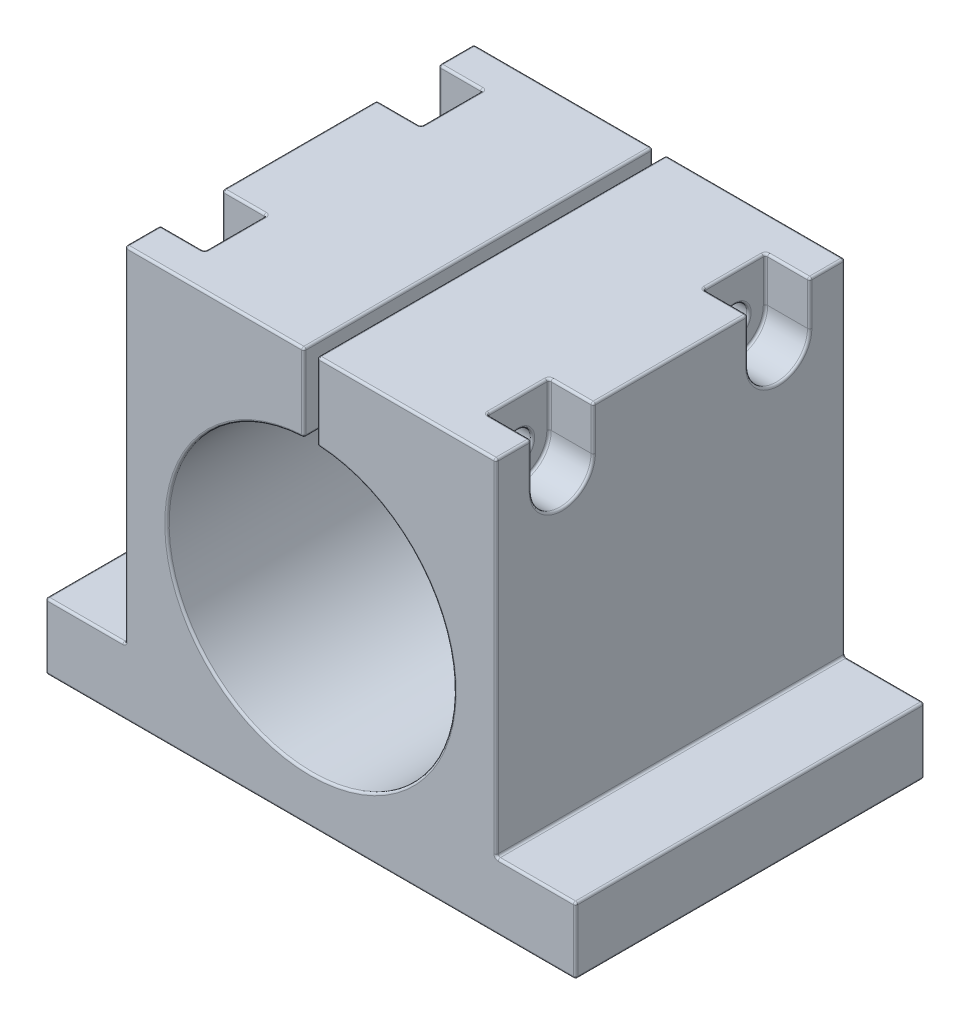
SolidWorks part; units mm, degrees
ref_plane "Спереди" through (0, 0, 0) normal (0, 0, 1) x (1, 0, 0)
ref_plane "Сверху" through (0, 0, 0) normal (0, 1, 0) x (1, 0, 0)
ref_plane "Справа" through (0, 0, 0) normal (1, 0, 0) x (0, 0, -1)
sketch "Эскиз1" plane through (0, 0, 0) normal (0, 0, 1) x (1, 0, 0)
  line L0 (158.9731, 494.9046) -> (1058.9731, 494.9046) construction
  line L1 (0, 0) -> (0, -43) construction
  line L2 (60, -43) -> (-60, -43)
  line L3 (-60, -43) -> (-60, -28)
  line L4 (-60, -28) -> (-42, -28)
  line L5 (-42, -28) -> (-42, 50)
  line L6 (-42, 50) -> (-1.5, 50)
  line L7 (-1.5, 50) -> (-1.5, 32.4654)
  line L8 (1.5, 50) -> (1.5, 32.4654)
  line L9 (42, 50) -> (1.5, 50)
  line L10 (42, -28) -> (42, 50)
  line L11 (60, -28) -> (42, -28)
  line L12 (60, -43) -> (60, -28)
  circle A0 centre (0, 0) radius 32.5
  dimension "D1" = 65
  dimension "D2" = 3
  dimension "D3" = 78
  dimension "D4" = 15
  dimension "D5" = 84
  dimension "D6" = 120
  dimension "D7" = 43
extrude "Бобышка-Вытянуть1" add sketch "Эскиз1" along normal mid plane 79 contours A0 L7 L6 L5 L4 L3 L2 L12 L11 L10 L9 L8
sketch "Эскиз2" plane through (-42, 0, 0) normal (-1, 0, 0) x (0, 0, 1)
  line L0 (39.5, 50) -> (-39.5, 50) construction
  line L1 (-31.5, 50) -> (-17.5, 50)
  line L2 (-31.5, 50) -> (-31.5, 40)
  line L3 (-31.5, 40) -> (-17.5, 40)
  line L4 (-17.5, 50) -> (-17.5, 40)
  line L5 (-39.5, -28) -> (-39.5, 50) construction
  line L6 (17.5, 50) -> (31.5, 50)
  line L7 (17.5, 50) -> (17.5, 40)
  line L8 (17.5, 40) -> (31.5, 40)
  line L9 (31.5, 50) -> (31.5, 40)
  line L10 (39.5, -28) -> (39.5, 50) construction
  circle A0 centre (-24.5, 40) radius 7
  circle A1 centre (24.5, 40) radius 7
  line M8 (39.5, 50) -> (-39.5, 50)
  dimension "D1" = 8
  dimension "D2" = 8
  dimension "D3" = 14
  dimension "D4" = 10
extrude "Вырез-Вытянуть1" cut sketch "Эскиз2" against normal blind 10 contours L3 A0 | A0 L4 L2 M8 | L8 A1 | L8 A1 | A1 L9 L7 M8
sketch "Эскиз3" plane through (42, 0, 0) normal (1, 0, 0) x (0, 0, -1)
  line L6 (-31.5, 50) -> (-31.5, 40)
  line L7 (-17.5, 50) -> (-31.5, 50)
  line L8 (-17.5, 40) -> (-17.5, 50)
  line L9 (-31.5, 50) -> (-31.5, 40)
  line L10 (-17.5, 50) -> (-31.5, 50)
  line L11 (-17.5, 40) -> (-17.5, 50)
  line L15 (17.5, 50) -> (17.5, 40)
  line L16 (31.5, 50) -> (17.5, 50)
  line L17 (31.5, 40) -> (31.5, 50)
  line L18 (17.5, 50) -> (17.5, 40)
  line L19 (31.5, 50) -> (17.5, 50)
  line L20 (31.5, 40) -> (31.5, 50)
  arc A2 (-31.5, 40) -> (-17.5, 40) centre (-24.5, 40) ccw
  arc A3 (-31.5, 40) -> (-17.5, 40) centre (-24.5, 40) ccw
  arc A5 (17.5, 40) -> (31.5, 40) centre (24.5, 40) ccw
  arc A6 (17.5, 40) -> (31.5, 40) centre (24.5, 40) ccw
  dimension "D1" = 0
  dimension "D2" = 0
extrude "Вырез-Вытянуть2" cut sketch "Эскиз3" against normal blind 10
sketch "Эскиз4" plane through (-32, 0, 0) normal (-1, 0, 0) x (0, 0, 1)
  circle A0 centre (-24.5, 40) radius 3.25
  circle A1 centre (24.5, 40) radius 3.25
  dimension "D1" = 6.5
  dimension "D2" = 6.5
extrude "Вырез-Вытянуть3" cut sketch "Эскиз4" against normal through all
fillet "Скругление1" radius 0.5 80 edges at (42, 45, -31.5) (42, 45, 31.5) (42, 33, 24.5) (42, 45, 17.5) (42, 45, -17.5) (42, 33, -24.5) (42, -28, 0) (1.5, 41.2327, 39.5) (42, 11, 39.5) (51, -28, 39.5) (0, -43, 39.5) (-1.5, 41.2327, 39.5) (-42, 45, 17.5) (-42, 33, 24.5) (-42, 45, 31.5) (-42, 11, 39.5) (-42, 45, -31.5) (-42, 33, -24.5) (-42, 45, -17.5) (-37, 50, -31.5) (-42, 50, -35.5) (-1.5, 50, 0) (-21.75, 50, 39.5) (-42, 50, 35.5) (-37, 50, 31.5) (-37, 50, 17.5) (-42, 50, 0) (-37, 50, -17.5) (37, 50, 17.5) (37, 50, 31.5) (42, 50, 35.5) (21.75, 50, 39.5) (1.5, 50, 0) (42, 50, -35.5) (37, 50, -31.5) (37, 50, -17.5) (42, 50, 0) (32, 45, -17.5) (32, 50, -24.5) (32, 45, -31.5) (32, 33, -24.5) (32, 43.25, -24.5) (32, 45, 31.5) (32, 50, 24.5) (32, 45, 17.5) (32, 33, 24.5) (32, 43.25, 24.5) (60, -43, 0) (60, -35.5, 39.5) (60, -28, 0) (1.5, 32.4654, 0) (0, -32.5, 39.5) (-1.5, 32.4654, 0) (-1.5, 41.2327, -39.5) (-21.75, 50, -39.5) (-42, 11, -39.5) (0, -43, -39.5) (60, -35.5, -39.5) (51, -28, -39.5) (42, 11, -39.5) (21.75, 50, -39.5) (1.5, 41.2327, -39.5) (0, -32.5, -39.5) (-60, -35.5, 39.5) (-60, -43, 0) (-60, -35.5, -39.5) (-42, -28, 0) (-51, -28, 39.5) (-60, -28, 0) (-51, -28, -39.5) (-32, 45, 17.5) (-32, 50, 24.5) (-32, 45, 31.5) (-32, 33, 24.5) (-32, 36.75, 24.5) (-32, 45, -31.5) (-32, 50, -24.5) (-32, 45, -17.5) (-32, 33, -24.5) (-32, 36.75, -24.5)
